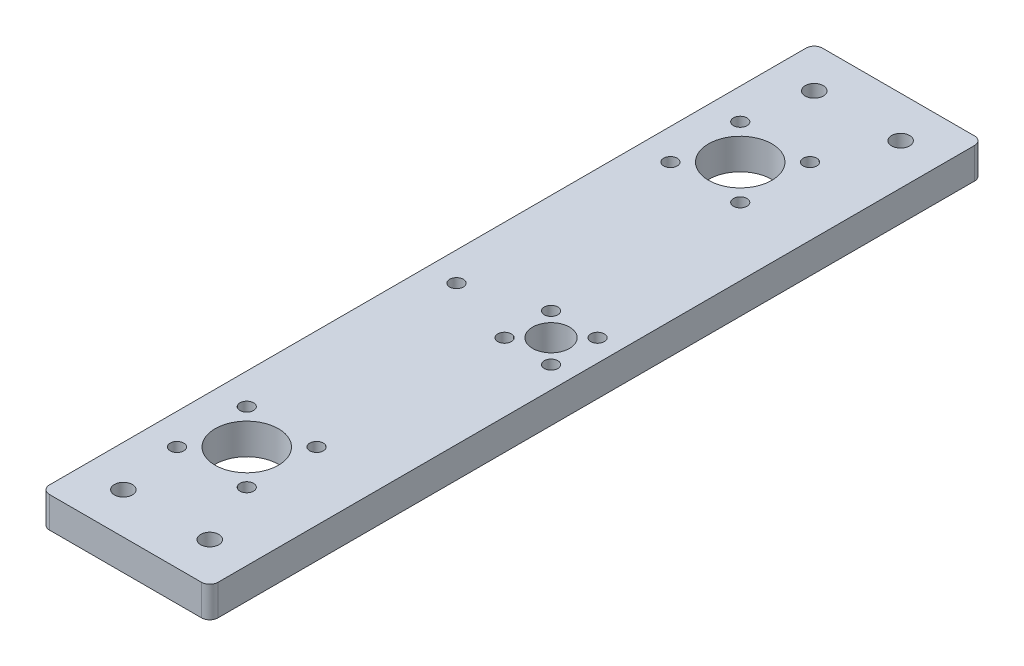
SolidWorks part; units mm, degrees
ref_plane "Front Plane" through (0, 0, 0) normal (0, 0, 1) x (1, 0, 0)
ref_plane "Top Plane" through (0, 0, 0) normal (0, 1, 0) x (1, 0, 0)
ref_plane "Right Plane" through (0, 0, 0) normal (1, 0, 0) x (0, 0, -1)
ref_plane "Plane1" through (0, 7.5, 0) normal (0, 1, 0) x (1, 0, 0)
sketch "Sketch1" plane through (0, 7.5, 0) normal (0, 1, 0) x (1, 0, 0)
  line L0 (18.5, 94) -> (-18.5, 94)
  line L1 (-20.5, 92) -> (-20.5, -92)
  line L2 (-18.5, -94) -> (18.5, -94)
  line L3 (20.5, -92) -> (20.5, 92)
  circle A0 centre (10.5, 84) radius 2.2
  circle A1 centre (-10.5, 84) radius 2.2
  circle A2 centre (10.5, -84) radius 2.2
  circle A3 centre (-10.5, -84) radius 2.2
  circle A4 centre (3.9853, 51.5147) radius 1.65
  circle A5 centre (15.1569, 5.6569) radius 1.65
  circle A6 centre (-12.9853, -68.4853) radius 1.65
  circle A7 centre (3.9853, -68.4853) radius 1.65
  circle A8 centre (-4.5, -60) radius 7.7
  circle A9 centre (9.5, 0) radius 4.5
  circle A10 centre (-12.9853, -51.5147) radius 1.65
  circle A11 centre (3.9853, -51.5147) radius 1.65
  circle A12 centre (3.9853, 68.4853) radius 1.65
  circle A13 centre (-12.9853, 68.4853) radius 1.65
  circle A14 centre (-12.9853, 51.5147) radius 1.65
  circle A15 centre (3.8431, 5.6569) radius 1.65
  circle A16 centre (3.8431, -5.6569) radius 1.65
  circle A17 centre (15.1569, -5.6569) radius 1.65
  circle A18 centre (-13.5, 0) radius 1.65
  circle A19 centre (-4.5, 60) radius 7.7
  arc A20 (-18.5, 94) -> (-20.5, 92) centre (-18.5, 92) ccw
  arc A21 (-20.5, -92) -> (-18.5, -94) centre (-18.5, -92) ccw
  arc A22 (18.5, -94) -> (20.5, -92) centre (18.5, -92) ccw
  arc A23 (20.5, 92) -> (18.5, 94) centre (18.5, 92) ccw
extrude "Boss-Extrude1" add sketch "Sketch1" against normal blind 7.5
